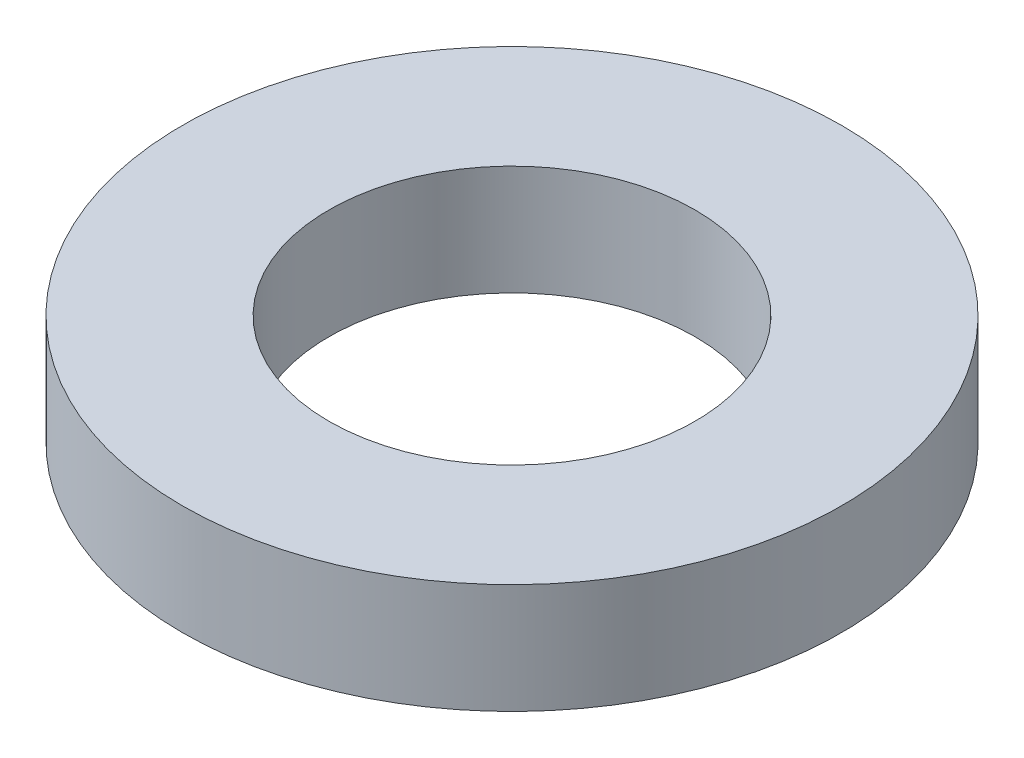
SolidWorks part; units mm, degrees
ref_plane "Front Plane" through (0, 0, 0) normal (0, 0, 1) x (1, 0, 0)
ref_plane "Top Plane" through (0, 0, 0) normal (0, 1, 0) x (1, 0, 0)
ref_plane "Right Plane" through (0, 0, 0) normal (1, 0, 0) x (0, 0, -1)
sketch "Sketch1" plane through (0, 0, 0) normal (0, 1, 0) x (1, 0, 0)
  circle A0 centre (0, 0) radius 4.5
  circle A1 centre (0, 0) radius 2.5
extrude "Boss-Extrude1" add sketch "Sketch1" along normal blind 1.5
